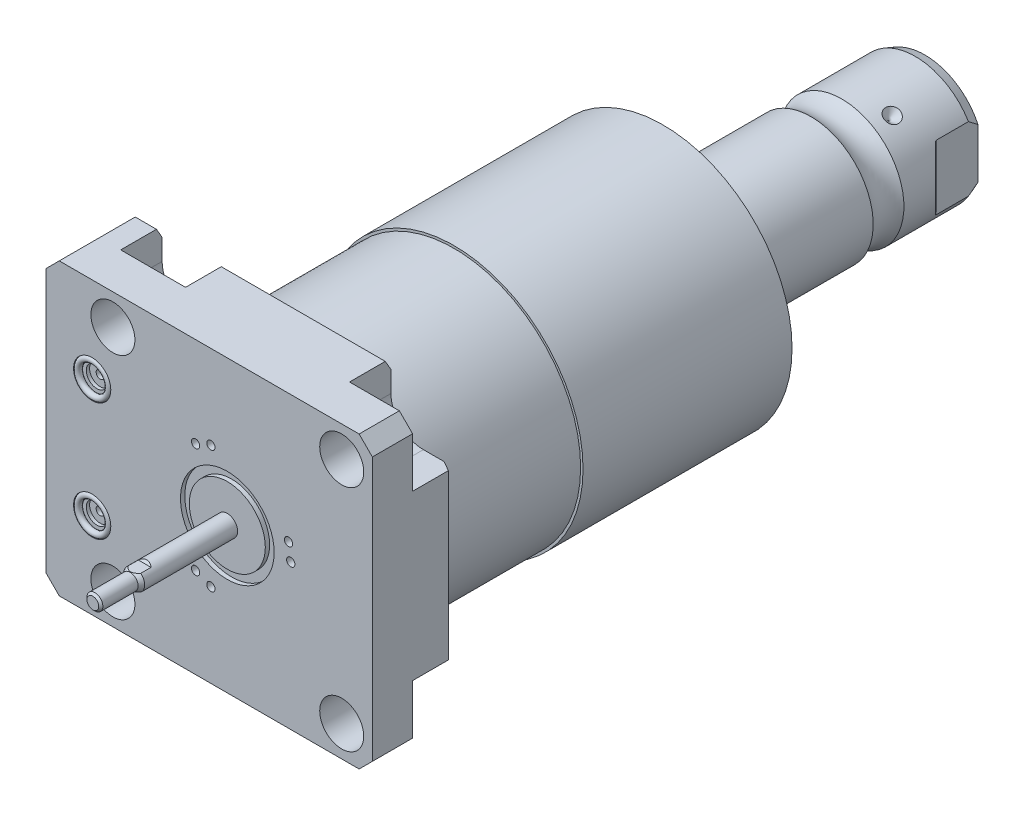
SolidWorks part; units mm, degrees
material "Alloy Steel"
ref_plane "Front Plane" through (0, 0, 0) normal (0, 0, 1) x (1, 0, 0)
ref_plane "Top Plane" through (0, 0, 0) normal (0, 1, 0) x (1, 0, 0)
ref_plane "Right Plane" through (0, 0, 0) normal (1, 0, 0) x (0, 0, -1)
sketch "Sketch1" plane through (0, 0, 0) normal (0, 0, 1) x (1, 0, 0)
  line L0 (-55.55, 44.45) -> (44.45, 44.45)
  line L1 (44.45, 44.45) -> (44.45, -44.45)
  line L2 (44.45, -44.45) -> (-55.55, -44.45)
  line L3 (-55.55, -44.45) -> (-55.55, 44.45)
  dimension "D1" = 100
  dimension "D2" = 88.9
  dimension "D3" = 44.45
  dimension "D4" = 44.45
extrude "Extrude1" add sketch "Sketch1" along normal blind 25.019
hole_wizard "Hole1" positions "Sketch22" profile "Sketch21" legacy end condition through all
sketch "Sketch22" plane through (0, 0, 0) normal (0, 0, -1) x (-1, 0, 0)
  line L0 (0, 0) -> (42.7441, 0) construction
  line L1 (0, 0.8532) -> (0, 27.5062) construction
  point P0 (-35.052, -35.052)
  point P9 (-35.052, 35.052)
  point P11 (35.052, 35.052)
  point P12 (35.052, -35.052)
  dimension "D1" = 35.052
  dimension "D2" = 35.052
sketch "Sketch21" plane through (35.052, -35.052, 0) normal (1, 0, 0) x (0, 1, 0)
  line L0 (0, 0) -> (0, 25.019)
  line L1 (0, 25.019) -> (6.7435, 25.019)
  line L2 (6.7435, 25.019) -> (6.7435, 0)
  line L3 (6.7435, 0) -> (0, 0)
  line L4 (0, 110) -> (0, -10) construction
  dimension "Diameter" = 13.487
  dimension "Depth" = 25.019
sketch "Sketch3" plane through (0, 0, 0) normal (0, 0, -1) x (-1, 0, 0)
  line L0 (-35.052, -25.1205) -> (-44.45, -25.1205)
  line L1 (-44.45, -44.45) -> (-44.45, -25.1205)
  line L2 (-44.45, 25.1205) -> (-44.45, 44.45)
  line L3 (-44.45, 25.1205) -> (-35.052, 25.1205)
  line L4 (-25.1205, 35.052) -> (-25.1205, 44.45)
  line L5 (-44.45, 44.45) -> (-25.1205, 44.45)
  line L6 (25.1205, 44.45) -> (25.1205, 35.052)
  line L7 (44.9835, 35.052) -> (44.9835, 44.45)
  line L8 (25.1205, 44.45) -> (44.9835, 44.45)
  line L9 (44.9835, -44.45) -> (25.1205, -44.45)
  line L10 (44.9835, -44.45) -> (44.9835, -35.052)
  line L11 (25.1205, -35.052) -> (25.1205, -44.45)
  line L12 (-25.1205, -44.45) -> (-44.45, -44.45)
  line L13 (-25.1205, -44.45) -> (-25.1205, -35.052)
  line L14 (-44.45, 44.45) -> (55.55, 44.45) construction
  line L15 (-44.45, -44.45) -> (-44.45, 44.45) construction
  line L16 (55.55, -44.45) -> (-44.45, -44.45) construction
  arc A0 (-25.1205, -35.052) -> (-35.052, -25.1205) centre (-35.052, -35.052) ccw
  arc A1 (-35.052, 25.1205) -> (-25.1205, 35.052) centre (-35.052, 35.052) ccw
  arc A2 (25.1205, 35.052) -> (44.9835, 35.052) centre (35.052, 35.052) ccw
  arc A3 (44.9835, -35.052) -> (25.1205, -35.052) centre (35.052, -35.052) ccw
  circle A8 centre (-35.052, 35.052) radius 6.7435 construction
  circle A9 centre (-35.052, -35.052) radius 6.7435 construction
  circle A10 centre (35.052, -35.052) radius 6.7435 construction
  circle A11 centre (35.052, 35.052) radius 6.7435 construction
  dimension "D1" = 9.9315
extrude "Cut-Extrude2" cut sketch "Sketch3" against normal blind 12.7
ref_plane "Plane16" through (0, 0, 12.014) normal (0, 0, 1) x (1, 0, 0)
sketch "Sketch23" plane through (0, 0, 12.014) normal (0, 0, 1) x (1, 0, 0)
  line L0 (-11.9397, -13.0048) -> (-61.0013, -13.0048) construction
  line L1 (-55.55, -23.749) -> (-55.296, -23.749)
  line L3 (-55.296, -23.749) -> (-55.296, -19.6596)
  line L4 (-55.296, -19.6596) -> (-54.5848, -18.9484)
  line L5 (-54.5848, -18.9484) -> (-41.1228, -18.9484)
  line L6 (-41.1228, -18.9484) -> (-41.1228, -13.0048)
  line L7 (-41.1228, -13.0048) -> (-55.55, -13.0048)
  line L8 (-55.55, -13.0048) -> (-55.55, -23.749)
  line L10 (-55.55, 44.45) -> (-55.55, -44.45) construction
  dimension "D1" = 21.4884
  dimension "D2" = 0.254
  dimension "D3" = 45
  dimension "D4" = 13.3096
  dimension "D5" = 11.8872
  dimension "D6" = 14.1732
  dimension "D7" = 13.0048
revolve "Cut-Revolve5" cut sketch "Sketch23" angle 360 about L0
mirror "Mirror1" about plane through (0, 0, 0) normal (0, 1, 0) of "Cut-Revolve5"
sketch "Sketch6" plane through (0, 0, 25.019) normal (0, 0, 1) x (1, 0, 0)
  line L0 (0, 0) -> (-71.0417, 0) construction
  circle A0 centre (-41.402, -18.11) radius 5.7023
  circle A1 centre (-41.402, 18.11) radius 5.7023
  dimension "D4" = 11.4046
  dimension "D1" = 18.11
  dimension "D2" = 36.22
  dimension "D3" = 41.402
extrude "Cut-Extrude3" cut sketch "Sketch6" against normal blind 1.4478
sketch "Sketch7" plane through (0, 0, 23.5712) normal (0, 0, 1) x (1, 0, 0)
  circle A0 centre (-41.402, 18.11) radius 3.2512
  circle A1 centre (-41.402, -18.11) radius 3.2512
  circle A2 centre (-41.402, 18.11) radius 5.7023 construction
  circle A3 centre (-41.402, -18.11) radius 5.7023 construction
  dimension "D1" = 6.5024
extrude "Cut-Extrude4" cut sketch "Sketch7" against normal blind 1.016
sketch "Sketch8" plane through (0, 0, 22.5552) normal (0, 0, 1) x (1, 0, 0)
  circle A0 centre (-41.402, 18.11) radius 1.2446
  circle A1 centre (-41.402, -18.11) radius 1.2446
  circle A2 centre (-41.402, 18.11) radius 5.7023 construction
  circle A3 centre (-41.402, -18.11) radius 5.7023 construction
  dimension "D1" = 2.4892
extrude "Cut-Extrude5" cut sketch "Sketch8" against normal blind 11.9888
ref_plane "Plane17" through (0, 18.11, 0) normal (0, 1, 0) x (-1, 0, 0)
sketch "Sketch9" plane through (-41.656, 18.11, 23.5712) normal (0, 1, 0) x (1, 0, 0)
  line L0 (0.254, -1.9469) -> (0.254, 0.0927) construction
  line L3 (-5.4483, 0) -> (5.9563, 0) construction
  line L4 (0.254, 13.0048) -> (0.254, 1.016) construction
  circle A0 centre (5.0292, -0.9271) radius 0.9271
  dimension "D1" = 1.8542
  dimension "D2" = 9.5504
revolve "Revolve1" add sketch "Sketch9" angle 360 about L0
mirror "Mirror2" about plane through (0, 0, 0) normal (0, 1, 0) of bodies 116
chamfer "Chamfer1" distance 4.064 angle 45 4 edges at (44.45, -44.45, 18.8595) (44.45, 44.45, 18.8595) (-55.55, 44.45, 12.5095) (-55.55, -44.45, 12.5095)
chamfer "Chamfer2" distance 3.0226 angle 30 5 edges at (-48.2347, -44.45, 0) (0, -44.45, 0) (44.45, 0, 0) (-48.2347, 44.45, 0) (0, 44.45, 0)
sketch "Sketch24" plane through (0, 0, 0) normal (1, 0, 0) x (0, 0, -1)
  line L0 (0, 0) -> (113.9127, 0) construction
  line L1 (0, 0) -> (0, 38.786)
  line L2 (0, 38.786) -> (44.45, 38.786)
  line L3 (44.45, 38.786) -> (44.45, 39.5225)
  line L4 (44.45, 39.5225) -> (108.4839, 39.5225)
  line L5 (108.4839, 39.5225) -> (112.268, 25.4)
  line L6 (112.268, 25.4) -> (112.268, 0)
  line L7 (112.268, 0) -> (0, 0)
  dimension "D1" = 77.572
  dimension "D2" = 44.45
  dimension "D3" = 79.045
  dimension "D4" = 50.8
  dimension "D5" = 15
  dimension "D6" = 112.268
revolve "Revolve4" add sketch "Sketch24" angle 360 about L0
sketch "Sketch17" plane through (0, 0, 0) normal (1, 0, 0) x (0, 0, -1)
  line L0 (112.268, 0) -> (112.268, -19.05)
  line L1 (112.268, -19.05) -> (153.8149, -19.05)
  line L2 (163.2291, -19.05) -> (185.776, -19.05)
  line L3 (188.697, -17.9868) -> (188.697, 0)
  line L4 (188.697, 0) -> (112.268, 0)
  line L5 (130.8989, 0) -> (0.816, 0) construction
  line L6 (112.268, -25.4) -> (112.268, 25.4) construction
  line L7 (-25.019, -40.386) -> (-25.019, 40.386) construction
  line L8 (188.697, -17.9868) -> (185.776, -19.05)
  arc A0 (163.2291, -19.05) -> (153.8149, -19.05) centre (158.522, -25.4254) ccw
  dimension "D2" = 20
  dimension "D4" = 7.9248
  dimension "D5" = 35.0012
  dimension "D1" = 213.716
  dimension "D3" = 38.1
  dimension "D6" = 30.175
  dimension "D7" = 2.921
revolve "Revolve3" add sketch "Sketch17" angle 360 about L5
sketch "Sketch28" plane through (0, 0, 0) normal (0, 1, 0) x (1, 0, 0)
  line L0 (-34.3062, 169.19) -> (35.4095, 169.19) construction
  line L1 (-19.05, 171.603) -> (-16.637, 169.19)
  line L2 (-19.05, 185.776) -> (-19.05, 163.2291) construction
  line L3 (-16.637, 169.19) -> (-19.05, 169.19)
  line L4 (-19.05, 169.19) -> (-19.05, 171.603)
  arc A0 (-19.05, 153.8149) -> (-19.05, 163.2291) centre (-25.4254, 158.522) ccw construction
  dimension "D3" = 10.668
  dimension "D1" = 45
  dimension "D2" = 4.826
revolve "Cut-Revolve6" cut sketch "Sketch28" angle 360 about L0
pattern_circular "CirPattern1" count 3 over 360 about axis through (0, 0, -130.8989) along (0, 0, -1) of "Cut-Revolve6"
hole_wizard "Hole2" positions "Sketch33" profile "Sketch32" legacy
sketch "Sketch33" plane through (0, 0, -188.697) normal (0, 0, -1) x (-1, 0, 0)
  circle A0 centre (0, 0) radius 19.05 construction
  point P0 (0, 0)
sketch "Sketch32" plane through (0, 0, -188.697) normal (1, 0, 0) x (0, 1, 0)
  line L0 (0, 0) -> (0, 29.5665)
  line L1 (0, 29.5665) -> (6.9342, 25.4)
  line L2 (6.9342, 25.4) -> (6.9342, 0)
  line L4 (6.9342, 0) -> (0, 0)
  line L6 (0, 29.5665) -> (-6.9342, 25.4) construction
  line L7 (0, -4.2442) -> (0, 117.3081) construction
  dimension "Diameter" = 13.8684
  dimension "Depth" = 25.4
  dimension "Drill Angle" = 118
sketch "Sketch34" plane through (0, 0, 0) normal (0, 1, 0) x (0, 0, -1)
  line L0 (0, 0) -> (211.3651, 0) construction
  line L1 (172.9129, 19.05) -> (175.4582, 16.5047)
  line L3 (175.997, 16.2815) -> (188.697, 16.2815)
  line L4 (188.697, -17.9868) -> (188.697, 17.9868) construction
  line L5 (188.697, 16.2815) -> (188.697, 19.05)
  line L6 (188.697, 19.05) -> (172.9129, 19.05)
  line L7 (188.697, -19.05) -> (172.9129, -19.05)
  line L8 (188.697, -16.2815) -> (188.697, -19.05)
  line L9 (175.997, -16.2815) -> (188.697, -16.2815)
  line L10 (172.9129, -19.05) -> (175.4582, -16.5047)
  line L11 (185.776, 19.05) -> (171.603, 19.05) construction
  arc A0 (175.997, 16.2815) -> (175.4582, 16.5047) centre (175.997, 17.0435) cw
  arc A1 (175.997, -16.2815) -> (175.4582, -16.5047) centre (175.997, -17.0435) ccw
  dimension "D2" = 0.762
  dimension "D1" = 45
  dimension "D3" = 12.7
  dimension "D4" = 32.563
extrude "Cut-Extrude8" cut sketch "Sketch34" against normal through all and the other way through all
sketch "Sketch35" plane through (0, 0, 0) normal (1, 0, 0) x (0, 0, -1)
  line L0 (-1000, 0) -> (49000, 0) construction
  line L1 (-25.019, 0) -> (-25.019, -3.175)
  line L2 (-25.019, -40.386) -> (-25.019, 40.386) construction
  line L3 (-25.019, -3.175) -> (-53.5111, -3.175)
  line L4 (-53.5111, -3.175) -> (-54.787, -2.4384)
  line L5 (-54.787, -2.4384) -> (-65.582, -2.4384)
  line L6 (-65.582, -2.4384) -> (-66.217, -1.8034)
  line L7 (-66.217, -1.8034) -> (-66.217, 0)
  line L8 (-66.217, 0) -> (-25.019, 0)
  line L9 (188.697, -17.9868) -> (188.697, -7.6446) construction
  dimension "D1" = 45
  dimension "D2" = 0.635
  dimension "D3" = 30
  dimension "D4" = 4.8768
  dimension "D5" = 6.35
  dimension "D6" = 11.43
  dimension "D7" = 254.914
revolve "Revolve5" add sketch "Sketch35" angle 360 about L0
sketch "Sketch36" plane through (0, 0, 0) normal (1, 0, 0) x (0, 0, -1)
  line L0 (-1000, 0) -> (49000, 0) construction
  line L1 (-49.6689, -3.175) -> (-50.342, -2.5019)
  line L2 (-53.5111, -3.175) -> (-25.019, -3.175) construction
  line L3 (-50.342, -2.5019) -> (-66.217, -2.5019)
  line L4 (-66.217, 1.8034) -> (-66.217, -1.8034) construction
  line L5 (-49.6689, -3.175) -> (-66.217, -3.175)
  line L6 (-66.217, -3.175) -> (-66.217, -2.5019)
  line L7 (-49.6689, 3.175) -> (-50.342, 2.5019)
  line L8 (-50.342, 2.5019) -> (-66.217, 2.5019)
  line L9 (-49.6689, 3.175) -> (-66.217, 3.175)
  line L10 (-66.217, 3.175) -> (-66.217, 2.5019)
  dimension "D1" = 45
  dimension "D2" = 5.0038
  dimension "D3" = 15.875
extrude "Cut-Extrude9" cut sketch "Sketch36" against normal mid plane 7.62
sketch "Sketch37" plane through (0, 0, 0) normal (1, 0, 0) x (0, 0, -1)
  line L0 (-1000, 0) -> (49000, 0) construction
  line L1 (-25.019, -40.386) -> (-25.019, 40.386) construction
  line L2 (-25.019, -11.6459) -> (-23.6982, -11.6459)
  line L3 (-25.019, -11.6459) -> (-25.019, -14.351)
  line L4 (-25.019, -14.351) -> (-23.6982, -14.351)
  line L5 (-23.6982, -11.6459) -> (-23.6982, -14.351)
  dimension "D1" = 23.2918
  dimension "D2" = 28.7021
  dimension "D3" = 1.3208
revolve "Cut-Revolve7" cut sketch "Sketch37" angle 360 about L0
sketch "Sketch38" plane through (0, 0, 25.019) normal (0, 0, 1) x (1, 0, 0)
  line L0 (-1000, 0) -> (49000, 0) construction
  line L1 (0, 0) -> (48296.2913, 12940.9523) construction
  line L2 (0, 0) -> (25000, 43301.2702) construction
  circle A0 centre (0, 0) radius 19.431 construction
  circle A1 centre (19.431, 0) radius 1.27
  circle A2 centre (18.7689, 5.0291) radius 1.27
  circle A3 centre (-5.0291, 18.7689) radius 1.27
  circle A4 centre (-9.7155, 16.8278) radius 1.27
  circle A5 centre (-9.7155, -16.8278) radius 1.27
  circle A6 centre (-5.0291, -18.7689) radius 1.27
  dimension "D3" = 38.8621
  dimension "D4" = 2.54
  dimension "D5" = 2.54
  dimension "D1" = 15
  dimension "D2" = 60
extrude "Cut-Extrude10" cut sketch "Sketch38" against normal blind 7.62
